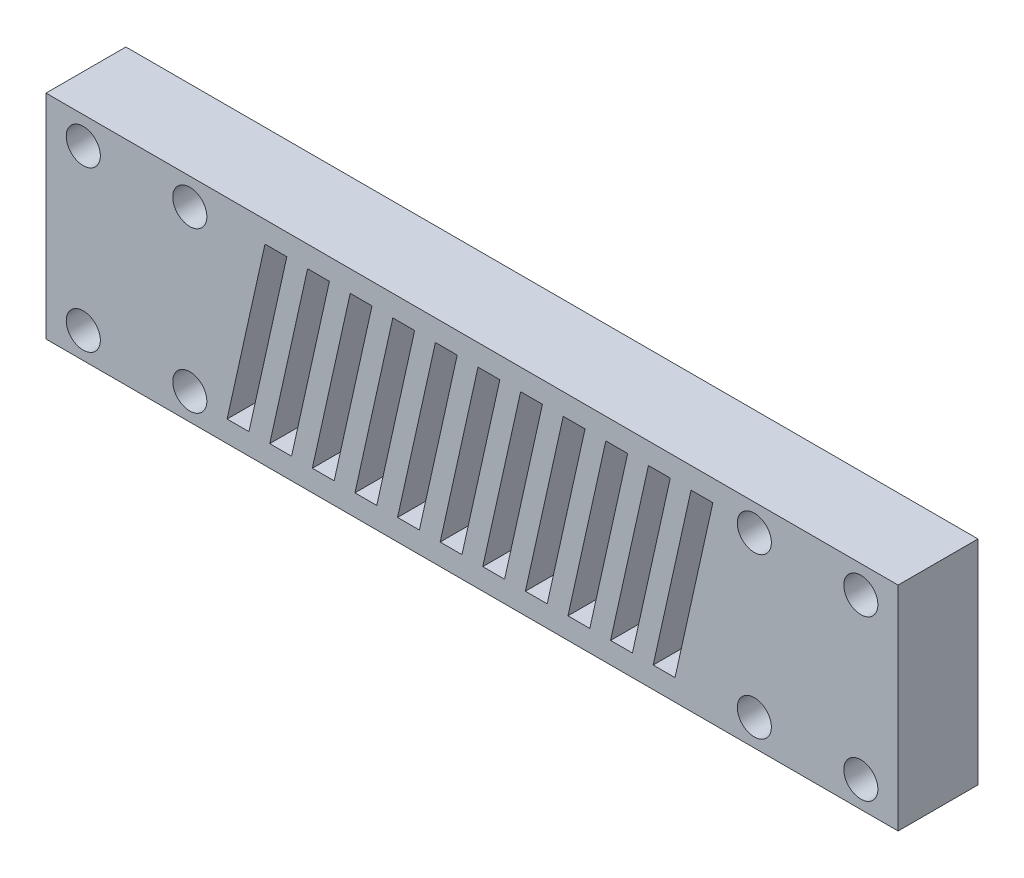
SolidWorks part; units mm, degrees
ref_plane "Front Plane" through (0, 0, 0) normal (0, 0, 1) x (1, 0, 0)
ref_plane "Top Plane" through (0, 0, 0) normal (0, 1, 0) x (1, 0, 0)
ref_plane "Right Plane" through (0, 0, 0) normal (1, 0, 0) x (0, 0, -1)
sketch "Sketch1" plane through (0, 0, 0) normal (0, 0, 1) x (1, 0, 0)
  line L0 (0, -0.3509) -> (38.7265, -0.3509) construction
  line L1 (-40, -10.3509) -> (40, -10.3509)
  line L2 (-40, 9.6491) -> (40, 9.6491)
  line L3 (0, 5.6779) -> (0, -5.9981) construction
  line L4 (-40, 9.6491) -> (-40, -10.3509)
  line L5 (40, 9.6491) -> (40, -10.3509)
  circle A0 centre (36.5, 7.0968) radius 1.6
  circle A1 centre (26.5, 7.1491) radius 1.6
  circle A2 centre (36.5, -7.9032) radius 1.6
  circle A3 centre (26.5, -7.8509) radius 1.6
  circle A4 centre (-26.5, -7.8509) radius 1.6
  circle A5 centre (-36.5, -7.9032) radius 1.6
  circle A6 centre (-26.5, 7.1491) radius 1.6
  circle A7 centre (-36.5, 7.0968) radius 1.6
  point P0 (0, 0)
  dimension "D1" = 3.2
  dimension "D2" = 3.2
  dimension "D3" = 3.2
  dimension "D4" = 3.2
  dimension "D5" = 10
  dimension "D6" = 15
  dimension "D7" = 15
  dimension "D8" = 10
  dimension "D9" = 63
  dimension "D10" = 63
  dimension "D11" = 63
  dimension "D12" = 63
  dimension "D13" = 73
  dimension "D14" = 73
  dimension "D15" = 53
  dimension "D16" = 53
  dimension "D17" = 7.5
  dimension "D18" = 10
  dimension "D19" = 10
  dimension "D20" = 36.5
  dimension "D21" = 40
  dimension "D22" = 40
  dimension "D23" = 40
  dimension "D24" = 40
  dimension "D25" = 36.5
extrude "Boss-Extrude4" add sketch "Sketch1" along normal blind 7.5
sketch "Sketch6" plane through (0, 0, 7.5) normal (0, 0, 1) x (1, 0, 0)
  line L0 (-19.441, 7.6491) -> (-22.9948, -8.3509)
  line L1 (-22.9948, -8.3509) -> (-20.946, -8.3509)
  line L2 (-20.946, -8.3509) -> (-17.3923, 7.6491)
  line L3 (-17.3923, 7.6491) -> (-19.441, 7.6491)
  line L4 (40, 9.6491) -> (-40, 9.6491) construction
  line L5 (-40, -10.3509) -> (40, -10.3509) construction
  line L6 (-13.3923, 7.6491) -> (-15.441, 7.6491)
  line L7 (-16.946, -8.3509) -> (-13.3923, 7.6491)
  line L8 (-15.441, 7.6491) -> (-18.9948, -8.3509)
  line L9 (-18.9948, -8.3509) -> (-16.946, -8.3509)
  line L10 (-9.3923, 7.6491) -> (-11.441, 7.6491)
  line L11 (-12.946, -8.3509) -> (-9.3923, 7.6491)
  line L12 (-11.441, 7.6491) -> (-14.9948, -8.3509)
  line L13 (-14.9948, -8.3509) -> (-12.946, -8.3509)
  line L14 (-5.3923, 7.6491) -> (-7.441, 7.6491)
  line L15 (-8.946, -8.3509) -> (-5.3923, 7.6491)
  line L16 (-7.441, 7.6491) -> (-10.9948, -8.3509)
  line L17 (-10.9948, -8.3509) -> (-8.946, -8.3509)
  line L18 (-1.3923, 7.6491) -> (-3.441, 7.6491)
  line L19 (-4.946, -8.3509) -> (-1.3923, 7.6491)
  line L20 (-3.441, 7.6491) -> (-6.9948, -8.3509)
  line L21 (-6.9948, -8.3509) -> (-4.946, -8.3509)
  line L22 (2.6077, 7.6491) -> (0.559, 7.6491)
  line L23 (-0.946, -8.3509) -> (2.6077, 7.6491)
  line L24 (0.559, 7.6491) -> (-2.9948, -8.3509)
  line L25 (-2.9948, -8.3509) -> (-0.946, -8.3509)
  line L26 (6.6077, 7.6491) -> (4.559, 7.6491)
  line L27 (3.054, -8.3509) -> (6.6077, 7.6491)
  line L28 (4.559, 7.6491) -> (1.0052, -8.3509)
  line L29 (1.0052, -8.3509) -> (3.054, -8.3509)
  line L30 (10.6077, 7.6491) -> (8.559, 7.6491)
  line L31 (7.054, -8.3509) -> (10.6077, 7.6491)
  line L32 (8.559, 7.6491) -> (5.0052, -8.3509)
  line L33 (5.0052, -8.3509) -> (7.054, -8.3509)
  line L34 (14.6077, 7.6491) -> (12.559, 7.6491)
  line L35 (11.054, -8.3509) -> (14.6077, 7.6491)
  line L36 (12.559, 7.6491) -> (9.0052, -8.3509)
  line L37 (9.0052, -8.3509) -> (11.054, -8.3509)
  line L38 (18.6077, 7.6491) -> (16.559, 7.6491)
  line L39 (15.054, -8.3509) -> (18.6077, 7.6491)
  line L40 (16.559, 7.6491) -> (13.0052, -8.3509)
  line L41 (13.0052, -8.3509) -> (15.054, -8.3509)
  line L42 (22.6077, 7.6491) -> (20.559, 7.6491)
  line L43 (19.054, -8.3509) -> (22.6077, 7.6491)
  line L44 (20.559, 7.6491) -> (17.0052, -8.3509)
  line L45 (17.0052, -8.3509) -> (19.054, -8.3509)
  dimension "D1" = 2
  dimension "D2" = 2
  dimension "D3" = 2
  dimension "D4" = 11
extrude "Cut-Extrude1" cut sketch "Sketch6" against normal blind 7.5
